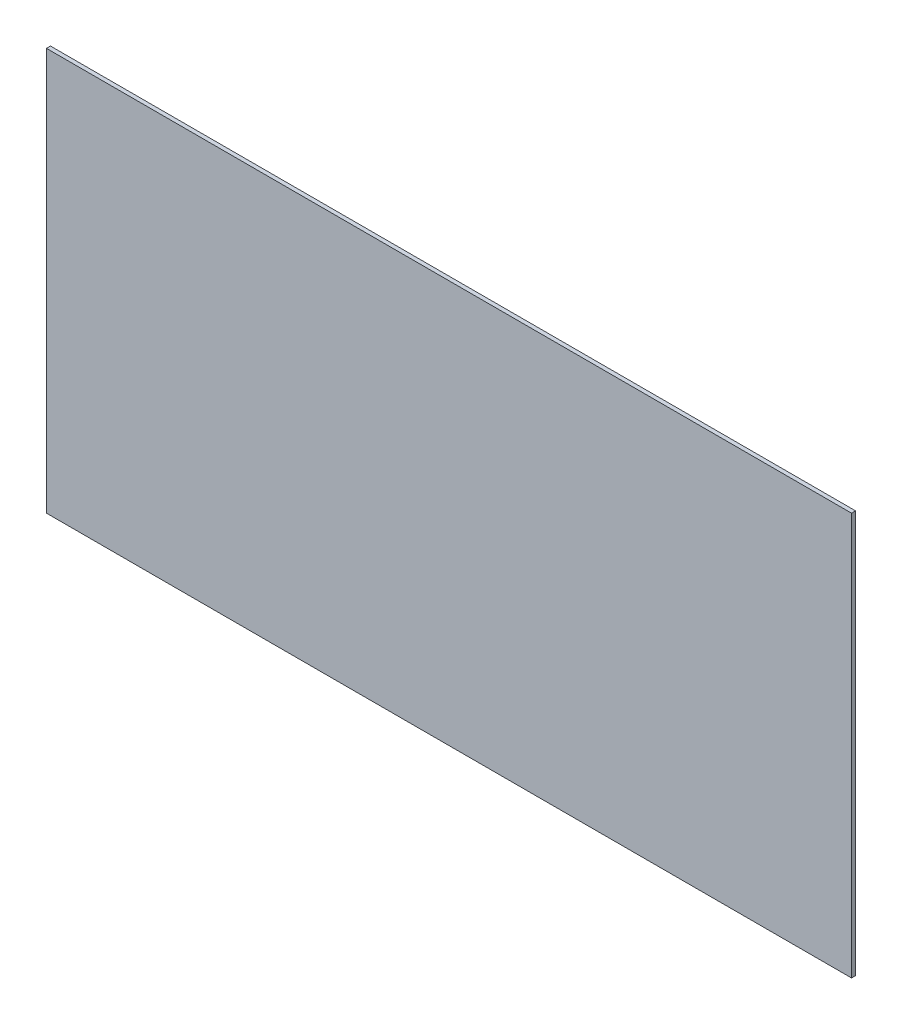
SolidWorks part; units mm, degrees
ref_plane "Front Plane" through (0, 0, 0) normal (0, 0, 1) x (1, 0, 0)
ref_plane "Top Plane" through (0, 0, 0) normal (0, 1, 0) x (1, 0, 0)
ref_plane "Right Plane" through (0, 0, 0) normal (1, 0, 0) x (0, 0, -1)
sketch "Sketch1" plane through (0, 0, 0) normal (0, 0, 1) x (1, 0, 0)
  line L0 (0, 0) -> (2000, 0)
  line L1 (2000, 0) -> (2000, 1000)
  line L2 (2000, 1000) -> (0, 1000)
  line L3 (0, 1000) -> (0, 0)
  dimension "D1" = 2000
  dimension "D2" = 1000
extrude "Boss-Extrude1" add sketch "Sketch1" against normal blind 10
